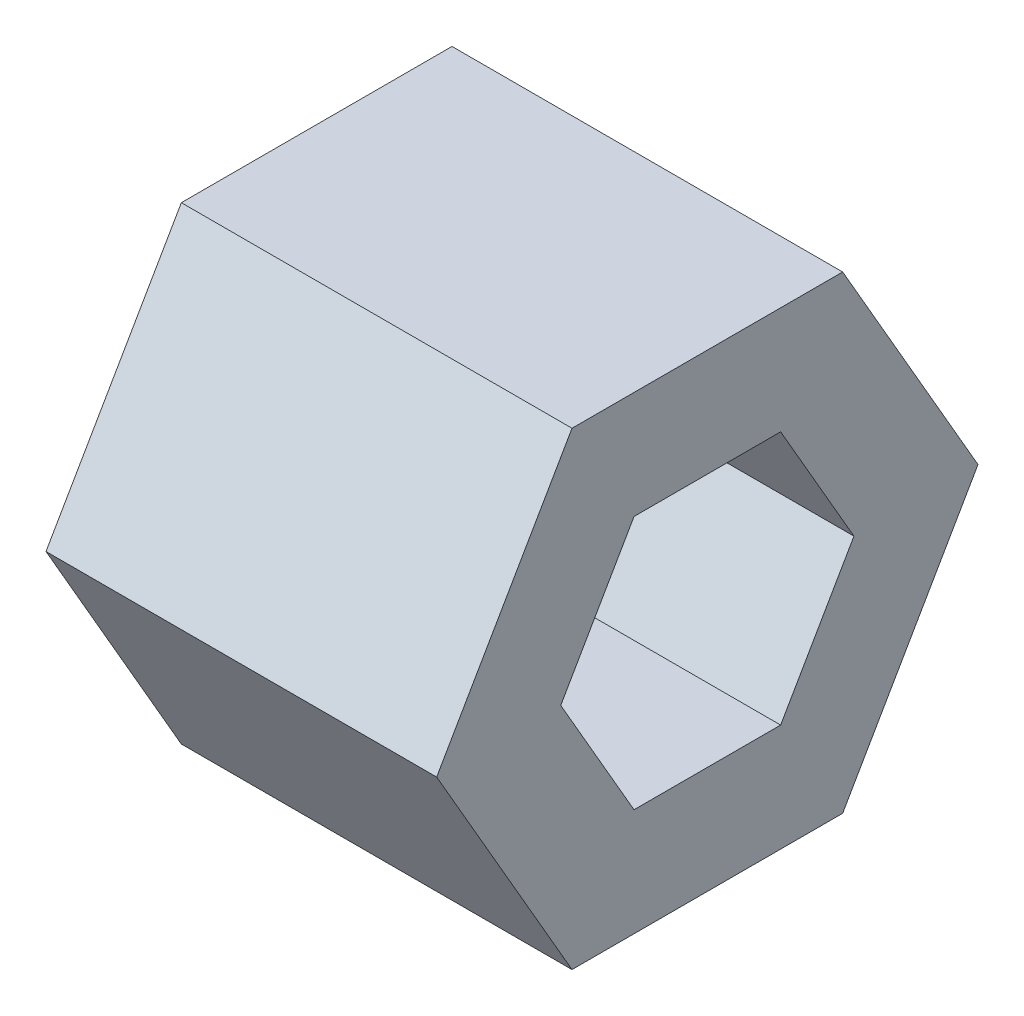
SolidWorks part; units mm, degrees
ref_plane "前视基准面" through (0, 0, 0) normal (0, 0, 1) x (1, 0, 0)
ref_plane "上视基准面" through (0, 0, 0) normal (0, 1, 0) x (1, 0, 0)
ref_plane "右视基准面" through (0, 0, 0) normal (1, 0, 0) x (0, 0, -1)
sketch "草图1" plane through (0, 0, 0) normal (1, 0, 0) x (0, 0, -1)
  line L1 (6.9282, 0) -> (3.4641, 6)
  line L2 (3.4641, 6) -> (-3.4641, 6)
  line L3 (-3.4641, 6) -> (-6.9282, 0)
  line L4 (-6.9282, 0) -> (-3.4641, -6)
  line L5 (-3.4641, -6) -> (3.4641, -6)
  line L6 (3.4641, -6) -> (6.9282, 0)
  circle A0 centre (0, 0) radius 6 construction
  dimension "D1" = 12
extrude "凸台-拉伸1" add sketch "草图1" along normal blind 10
sketch "草图2" plane through (10, 0, 0) normal (1, 0, 0) x (0, 0, -1)
  line L1 (3.7528, 0) -> (1.8764, 3.25)
  line L2 (1.8764, 3.25) -> (-1.8764, 3.25)
  line L3 (-1.8764, 3.25) -> (-3.7528, 0)
  line L4 (-3.7528, 0) -> (-1.8764, -3.25)
  line L5 (-1.8764, -3.25) -> (1.8764, -3.25)
  line L6 (1.8764, -3.25) -> (3.7528, 0)
  circle A0 centre (0, 0) radius 3.25 construction
  dimension "D1" = 6.5
extrude "切除-拉伸1" cut sketch "草图2" against normal blind 7
sketch "草图3" plane through (3, 0, 0) normal (1, 0, 0) x (0, 0, -1)
  circle A0 centre (0, 0) radius 1.5
extrude "切除-拉伸2" cut sketch "草图3" against normal blind 7
